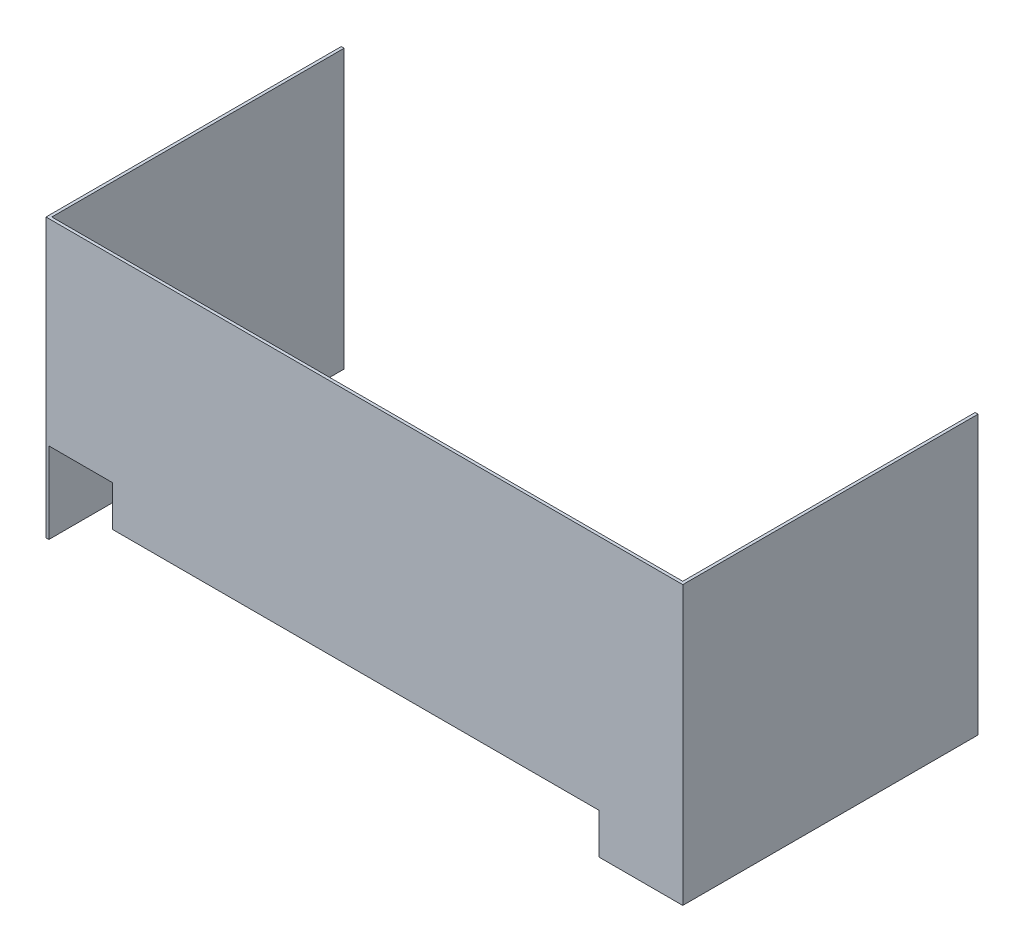
SolidWorks part; units mm, degrees
material "PC High Viscosity"
ref_plane "Front Plane" through (0, 0, 0) normal (0, 0, 1) x (1, 0, 0)
ref_plane "Top Plane" through (0, 0, 0) normal (0, 1, 0) x (1, 0, 0)
ref_plane "Right Plane" through (0, 0, 0) normal (1, 0, 0) x (0, 0, -1)
sketch "Sketch1" plane through (0, 0, 0) normal (0, 1, 0) x (1, 0, 0)
  line L0 (-349.25, -127) -> (-101.6, -127)
  line L1 (-31.75, -196.85) -> (222.25, -196.85) construction
  line L2 (-349.25, -127) -> (-349.25, 196.85)
  line L4 (349.25, -127) -> (349.25, 196.85)
  line L5 (-349.25, -196.85) -> (349.25, 196.85) construction
  line L6 (-349.25, 196.85) -> (349.25, -196.85) construction
  line L7 (-101.6, -127) -> (-31.75, -196.85) construction
  line L8 (222.25, -196.85) -> (292.1, -127) construction
  line L9 (292.1, -127) -> (349.25, -127)
  line L10 (-349.25, -196.85) -> (-349.25, -127) construction
  line L11 (-349.25, -196.85) -> (-31.75, -196.85) construction
  line L12 (222.25, -196.85) -> (349.25, -196.85) construction
  line L13 (349.25, -196.85) -> (349.25, -127) construction
  line L14 (-101.6, -127) -> (292.1, -127)
  point P0 (0, 0)
  dimension "D1" = 698.5
  dimension "D2" = 393.7
  dimension "D3" = 45
  dimension "D4" = 45
  dimension "D5" = 69.85
  dimension "D6" = 317.5
  dimension "D7" = 127
extrude "Extrude-Thin1" add sketch "Sketch1" along normal blind 304.8 thin thin type one direction wall 3.175
ref_plane "Plane1" [suppressed] through (-24.0849, 304.8, 193.675) normal (-1, 0, 0) x (0, 0, 1)
extrude "Cut-Extrude1" cut sketch "Sketch2" against normal through all
sketch "Sketch2" plane through (-139.5045, -186.6327, 127) normal (0, 0, 1) x (1, 0, 0)
  line L1 (-206.5705, 275.5327) -> (-136.7205, 275.5327)
  line L2 (-206.5705, 275.5327) -> (-206.5705, 186.6327)
  line L3 (-206.5705, 186.6327) -> (-136.7205, 186.6327)
  line L4 (-136.7205, 275.5327) -> (-136.7205, 186.6327)
sketch "Sketch3" plane through (0, 0, 123.825) normal (0, 0, -1) x (-1, 0, 0)
  line L0 (-346.075, 0) -> (276.225, 0) construction
  line L1 (-257.175, 0) -> (276.225, 0)
  line L2 (-257.175, 0) -> (-257.175, 44.45)
  line L3 (-257.175, 44.45) -> (276.225, 44.45)
  line L4 (276.225, 0) -> (276.225, 44.45)
  line L5 (276.225, 0) -> (276.225, 88.9) construction
  line L6 (276.225, 0) -> (276.225, 88.9) construction
  point P8 (276.225, 44.45)
  dimension "D1" = 533.4
extrude "Cut-Extrude2" cut sketch "Sketch3" against normal through all contours L3 L4 L1 L2
